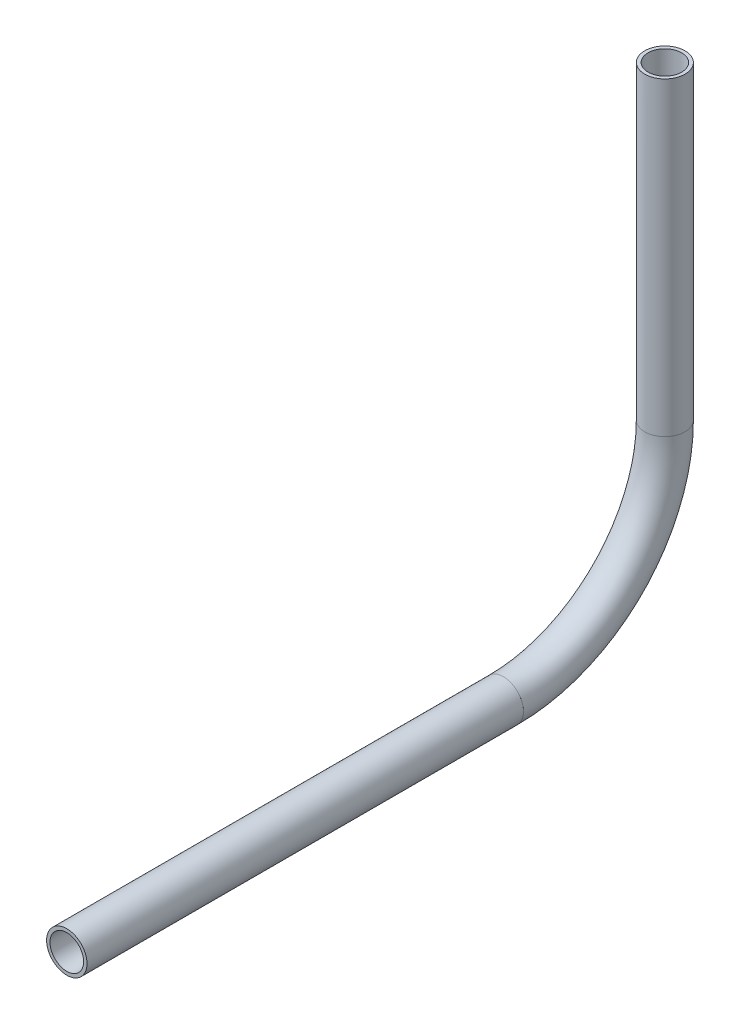
SolidWorks part; units mm, degrees
ref_plane "Front Plane" through (0, 0, 0) normal (0, 0, 1) x (1, 0, 0)
ref_plane "Top Plane" through (0, 0, 0) normal (0, 1, 0) x (1, 0, 0)
ref_plane "Right Plane" through (0, 0, 0) normal (1, 0, 0) x (0, 0, -1)
sketch "Sketch1" plane through (0, 0, 0) normal (1, 0, 0) x (0, 0, -1)
  line L0 (-303.1646, 599.96) -> (-165.8875, 599.96)
  line L1 (-115.0875, 650.76) -> (-115.0875, 748.1738)
  arc A0 (-165.8875, 599.96) -> (-115.0875, 650.76) centre (-165.8875, 650.76) ccw
  point P2 (-116.0262, 673.7051)
  point P6 (0, 0)
  point P7 (-115.0875, 748.1738)
  dimension "D1" = 50.8
other "Pipe 0.5 SCH 40(1)"
ref_plane "Plane1" through (0, 599.96, 303.1646) normal (0, 0, -1) x (0, 1, 0)
sketch "Sketch11" plane through (0, 599.96, 303.1646) normal (0, 0, -1) x (0, 1, 0)
  circle A0 centre (0, 0) radius 5.2832
  circle A1 centre (0, 0) radius 6.35
  point P5 (0, 0)
  dimension "In_dia" = 10.5664
  dimension "Out_dia" = 12.7
